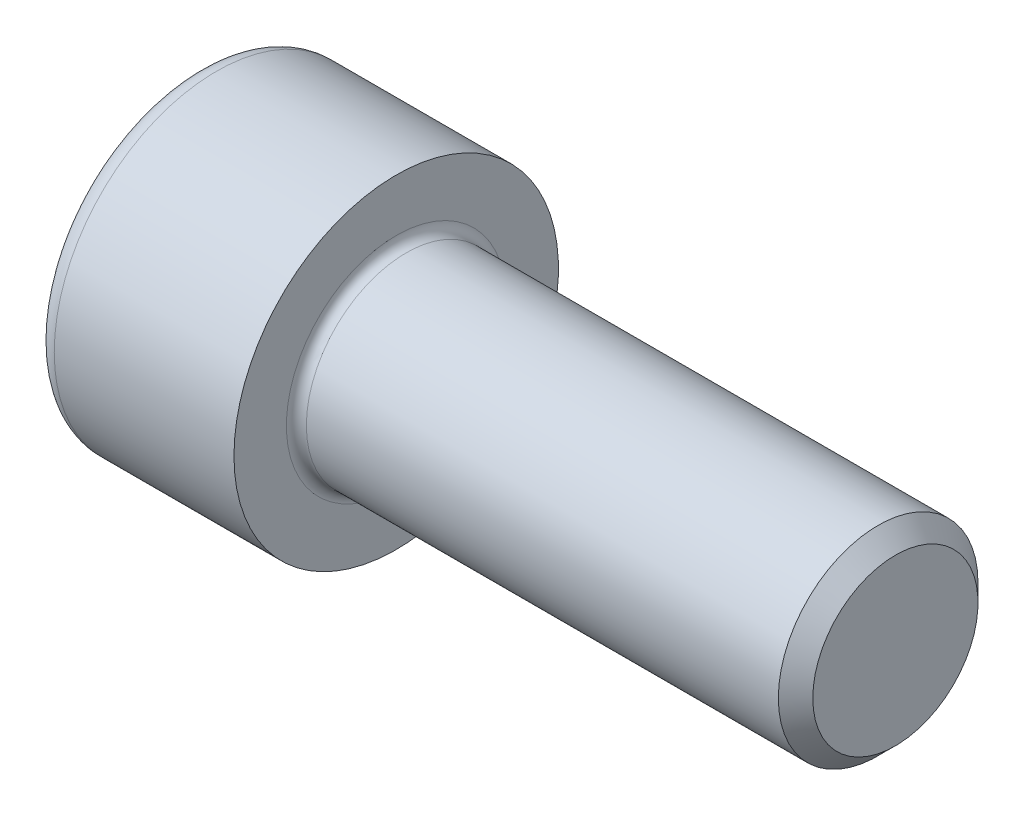
SolidWorks part; units mm, degrees
ref_plane "Plane1" through (0, 0, 0) normal (0, 0, 1) x (1, 0, 0)
ref_plane "Plane2" through (0, 0, 0) normal (0, 1, 0) x (1, 0, 0)
ref_plane "Plane3" through (0, 0, 0) normal (1, 0, 0) x (0, 0, -1)
sketch "BodySke" plane through (0, 0, 0) normal (0, 0, 1) x (1, 0, 0)
  line L0 (0, 0) -> (0, 6.5)
  line L1 (0, 6.5) -> (8, 6.5)
  line L2 (8, 6.5) -> (8, 4)
  line L3 (8, 4) -> (27.3095, 4)
  line L4 (28, 3.3095) -> (28, 0)
  line L5 (28, 0) -> (0, 0)
  line L6 (-31.75, 0) -> (127, 0) construction
  line L8 (28, 3.3095) -> (27.3095, 4)
  line L10 (28, -3.3095) -> (27.3095, -4) construction
  line L11 (9.25, 9.525) -> (9.25, 3.175) construction
  line L12 (8, 9.525) -> (8, 3.175) construction
  line L13 (-32, 9.525) -> (-32, 3.175) construction
  dimension "Diameter" = 8
  dimension "Head_ht" = 8
  dimension "Length" = 20
  dimension "Body_ch_ang" = 45
  dimension "Head_dia" = 13
  dimension "Minor_dia" = 6.619
  dimension "Advance" = 1.25
  dimension "Thread_nom" = 20
  dimension "Thread_length" = 60
revolve "Base-Revolve" add sketch "BodySke"
cosmetic thread "ThreadCosmetic"
fillet "Fillet1" radius 0.4 1 edges at (8, 0, 4)
fillet "Fillet2" radius 0.8 1 edges at (0, 0, 6.5)
sketch "Sketch2" plane through (0, 0, 0) normal (0, 0, 1) x (1, 0, 0)
  line L0 (0, 3.01) -> (4, 3.01)
  line L1 (4, 3.01) -> (5.7378, 0)
  line L2 (-31.75, 0) -> (127, 0) construction
  line L3 (5.7378, 0) -> (0, 0)
  line L4 (0, 0) -> (0, 3.01)
  line L6 (0, 0) -> (47.625, 0) construction
  dimension "D1" = 3.01
  dimension "D2" = 60
  dimension "Depth" = 4
revolve "Hex-PreBroach" cut sketch "Sketch2" angle 360 about L6
sketch "Sketch3" plane through (0, 0, 0) normal (-1, 0, 0) x (0, 0.5, 0.866)
  line L0 (1.7378, 3.01) -> (-1.7378, 3.01)
  line L1 (-1.7378, 3.01) -> (-3.4756, 0)
  line L2 (1.7378, 3.01) -> (3.4756, 0)
  line L3 (1.7378, -3.01) -> (3.4756, 0)
  line L4 (1.7378, -3.01) -> (-1.7378, -3.01)
  line L5 (-1.7378, -3.01) -> (-3.4756, 0)
  dimension "D1" = 3.01
  dimension "D2" = 3.01
  dimension "Hex_size" = 6.02
extrude "Hex" cut sketch "Sketch3" against normal blind 4
sketch "ThdSchSke" plane through (0, 0, 0) normal (0, 0, 1) x (1, 0, 0)
  line L0 (11.75, -3.3095) -> (11.2665, -4)
  line L1 (11.75, -3.3095) -> (12.2335, -4)
  line L2 (12.2335, -4) -> (12.2335, -5)
  line L3 (-3.175, 0) -> (5.1513, 0) construction
  line L4 (0, 5.7) -> (0, -5.7) construction
  line L5 (12.2335, -5) -> (11.2665, -5)
  line L6 (11.2665, -5) -> (11.2665, -4)
  dimension "Thread_minor" = 6.619
  dimension "Diameter" = 8
  dimension "Start" = 11.75
  dimension "SideAngle" = 55
  dimension "VeeAngle" = 70
  dimension "Overcut" = 10
revolve "ThreadSchematic" [suppressed] cut sketch "ThdSchSke" angle 360 about L3
pattern_linear "ThdSchPat" [suppressed]
equation "\"D2@Sketch3\" = \"Hex_size@Sketch3\" / 2"
equation "\"D1@Sketch3\" = \"Hex_size@Sketch3\" / 2"
equation "\"D1@Sketch2\" = \"Hex_size@Sketch3\" / 2"
equation "\"Thread_minor@ThreadCosmetic\"  =  \"Minor_dia@BodySke\""
equation "\"Depth@Sketch2\" =  \"Key_eng@Hex\""
equation "\"Thread_length@ThreadCosmetic\" = ((sgn( (\"Length@BodySke\" - \"Advance@BodySke\" * 3.0) - \"Thread_nom@BodySke\" )-1)*( (\"Length@BodySke\" - \"Advance@BodySke\" * 3.0) - \"Thread_nom@BodySke\" ))/-2+ \"Thread_nom@BodySke\""
equation "\"Thread_minor@ThdSchSke\" = \"Minor_dia@BodySke\""
equation "\"Diameter@ThdSchSke\" = \"Diameter@BodySke\""
equation "\"Overcut@ThdSchSke\" = \"Diameter@BodySke\" * 1.25"
equation "\"Start@ThdSchSke\" = \"Head_ht@BodySke\" + \"Length@BodySke\" - \"Thread_length@ThreadCosmetic\"  '---Non-countersunk---"
equation "\"Num_threads@ThdSchPat\" = int( \"Thread_length@ThreadCosmetic\" / \"Advance@BodySke\" + 0.999 )  + 1"
equation "\"Advance@ThdSchPat\" = \"Thread_length@ThreadCosmetic\" /  (\"Num_threads@ThdSchPat\" - 1) 'relax it"
equation "\"Num_threads@ThdSchPat\" = \"Num_threads@ThdSchPat\" - sgn( \"Num_threads@ThdSchPat\" - 1) '---chamfered tips only---"
